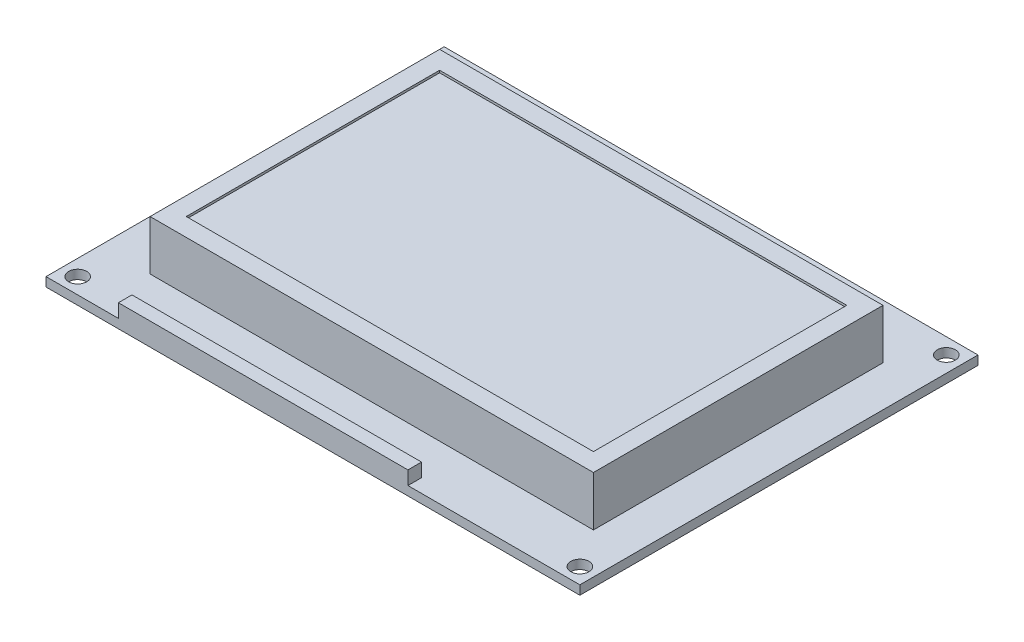
SolidWorks part; units mm, degrees
ref_plane "Front Plane" through (0, 0, 0) normal (0, 0, 1) x (1, 0, 0)
ref_plane "Top Plane" through (0, 0, 0) normal (0, 1, 0) x (1, 0, 0)
ref_plane "Right Plane" through (0, 0, 0) normal (1, 0, 0) x (0, 0, -1)
sketch "Sketch1" plane through (0, 0, 0) normal (0, 1, 0) x (1, 0, 0)
  line L1 (0, 0) -> (93.6625, 0)
  line L2 (0, 0) -> (0, 69.85)
  line L3 (0, 69.85) -> (93.6625, 69.85)
  line L4 (93.6625, 0) -> (93.6625, 69.85)
  line L5 (2.7781, 67.0719) -> (90.8844, 67.0719) construction
  line L6 (2.7781, 67.0719) -> (2.7781, 2.7781) construction
  line L7 (2.7781, 2.7781) -> (90.8844, 2.7781) construction
  line L8 (90.8844, 67.0719) -> (90.8844, 2.7781) construction
  line L9 (0, 69.85) -> (2.7781, 69.85) construction
  line L10 (0, 69.85) -> (0, 67.0719) construction
  line L11 (0, 67.0719) -> (2.7781, 67.0719) construction
  line L12 (2.7781, 69.85) -> (2.7781, 67.0719) construction
  line L13 (90.8844, 2.7781) -> (93.6625, 2.7781) construction
  line L14 (90.8844, 2.7781) -> (90.8844, 0) construction
  line L15 (90.8844, 0) -> (93.6625, 0) construction
  line L16 (93.6625, 2.7781) -> (93.6625, 0) construction
  circle A0 centre (2.7781, 67.0719) radius 1.5875
  circle A1 centre (90.8844, 67.0719) radius 1.5875
  circle A2 centre (2.7781, 2.7781) radius 1.5875
  circle A3 centre (90.8844, 2.7781) radius 1.5875
  dimension "D3" = 3.175
  dimension "D1" = 93.6625
  dimension "D2" = 69.85
  dimension "D4" = 2.7781
extrude "Boss-Extrude1" add sketch "Sketch1" along normal blind 1.5875
sketch "Sketch2" plane through (0, 1.5875, 0) normal (0, 1, 0) x (1, 0, 0)
  line L0 (93.6625, 0) -> (93.6625, 69.85) construction
  line L1 (8.7312, 9.525) -> (86.5187, 9.525)
  line L2 (8.7312, 9.525) -> (8.7312, 60.325)
  line L3 (8.7312, 60.325) -> (86.5187, 60.325)
  line L4 (86.5187, 9.525) -> (86.5187, 60.325)
  line L5 (93.6625, 69.85) -> (0, 69.85) construction
  dimension "D1" = 50.8
  dimension "D2" = 77.7875
  dimension "D3" = 7.1437
  dimension "D4" = 9.525
extrude "Boss-Extrude2" add sketch "Sketch2" along normal blind 8.7312
sketch "Sketch3" plane through (0, 1.5875, 0) normal (0, 1, 0) x (1, 0, 0)
  line L0 (0, 0) -> (93.6625, 0) construction
  line L1 (12.7, 0) -> (63.5, 0)
  line L2 (12.7, 0) -> (12.7, 2.3813)
  line L3 (12.7, 2.3813) -> (63.5, 2.3813)
  line L4 (63.5, 0) -> (63.5, 2.3813)
  line L5 (0, 69.85) -> (0, 0) construction
  dimension "D1" = 50.8
  dimension "D2" = 2.3813
  dimension "D3" = 12.7
extrude "Boss-Extrude3" add sketch "Sketch3" along normal blind 2.3813
sketch "Sketch4" plane through (0, 10.3187, 0) normal (0, 1, 0) x (1, 0, 0)
  line L0 (8.7312, 60.325) -> (8.7312, 9.525) construction
  line L1 (8.7312, 60.325) -> (11.9062, 60.325) construction
  line L2 (8.7312, 60.325) -> (8.7312, 57.15) construction
  line L3 (8.7312, 57.15) -> (11.9062, 57.15) construction
  line L4 (11.9062, 60.325) -> (11.9062, 57.15) construction
  line L5 (11.9062, 57.15) -> (83.3438, 57.15)
  line L6 (11.9062, 57.15) -> (11.9063, 12.7)
  line L7 (11.9063, 12.7) -> (83.3438, 12.7)
  line L8 (83.3438, 57.15) -> (83.3438, 12.7)
  line L9 (83.3438, 12.7) -> (86.5187, 12.7) construction
  line L10 (83.3438, 12.7) -> (83.3438, 9.525) construction
  line L11 (83.3438, 9.525) -> (86.5187, 9.525) construction
  line L12 (86.5187, 12.7) -> (86.5187, 9.525) construction
  dimension "D1" = 3.175
extrude "Cut-Extrude1" cut sketch "Sketch4" against normal blind 0.3969
